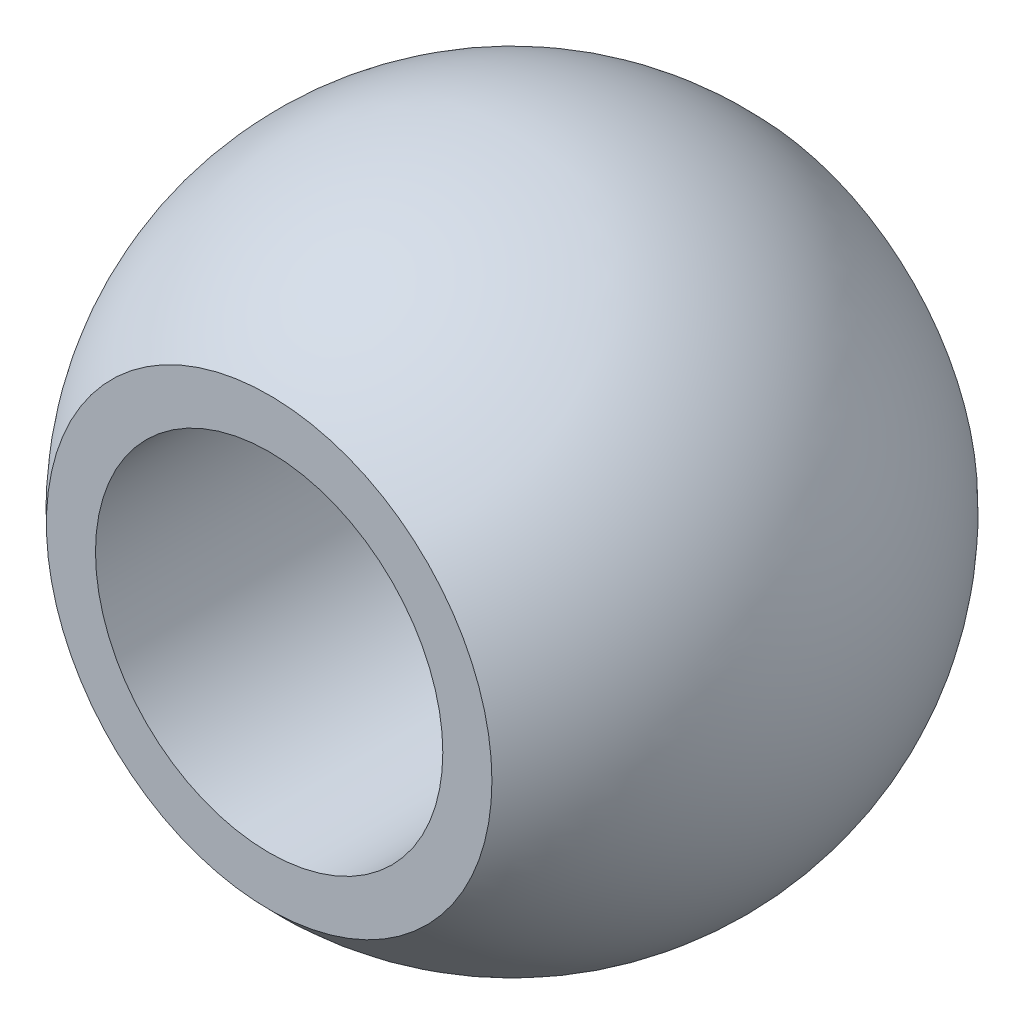
SolidWorks part; units mm, degrees
material "Plain Carbon Steel"
ref_plane "Front Plane" through (0, 0, 0) normal (0, 0, 1) x (1, 0, 0)
ref_plane "Top Plane" through (0, 0, 0) normal (0, 1, 0) x (1, 0, 0)
ref_plane "Right Plane" through (0, 0, 0) normal (1, 0, 0) x (0, 0, -1)
sketch "Sketch1" plane through (0, 0, 0) normal (1, 0, 0) x (0, 0, -1)
  line L0 (0, 0) -> (0, 61.9768) construction
  line L1 (-31.259, 0) -> (29.384, 0) construction
  line L2 (-5.5499, 5.0908) -> (-5.5499, 3.9688)
  line L3 (-5.5499, 3.9688) -> (5.5499, 3.9688)
  line L4 (5.5499, 3.9688) -> (5.5499, 5.0908)
  arc A0 (-5.5499, 5.0908) -> (5.5499, 5.0908) centre (0, 0) cw
  point P7 (0, 7.5311)
  dimension "D2" = 7.5311
  dimension "D1" = 11.0998
  dimension "D3" = 7.9375
revolve "Revolve1" add sketch "Sketch1"
sketch "Sketch2" plane through (0, 0, 0) normal (1, 0, 0) x (0, 0, -1)
  line L0 (-11.0989, 0) -> (11.0989, 0) construction
  arc A0 (5.5499, 5.0908) -> (-5.5499, 5.0908) centre (0, 0) ccw construction
  point P3 (0, 0)
